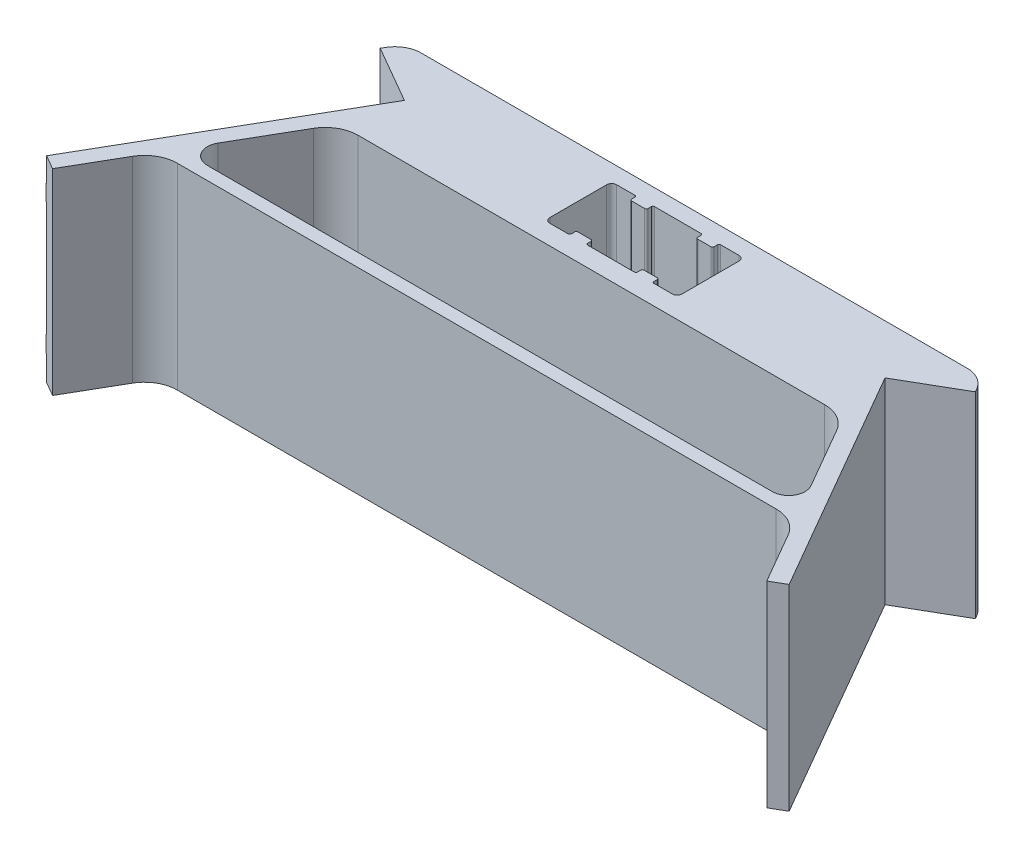
SolidWorks part; units mm, degrees
ref_plane "Front Plane" through (0, 0, 0) normal (0, 0, 1) x (1, 0, 0)
ref_plane "Top Plane" through (0, 0, 0) normal (0, 1, 0) x (1, 0, 0)
ref_plane "Right Plane" through (0, 0, 0) normal (1, 0, 0) x (0, 0, -1)
sketch "Sketch1" plane through (0, 0, 0) normal (0, 1, 0) x (1, 0, 0)
  line L0 (0, -61.4) -> (0, -111.1933) construction
  line L1 (0, 0) -> (-7.6, 0) construction
  line L2 (0, 0) -> (0, -20.4) construction
  line L3 (0, -20.4) -> (-7.1, -20.4) construction
  line L4 (-20.2, 0) -> (-20.2, -20.4) construction
  line L5 (0, 5) -> (-83.3812, 5)
  line L6 (-90.3094, 1) -> (-90.8868, 0)
  line L7 (-90.8868, 0) -> (-73.393, -10.1)
  line L8 (-73.393, -10.1) -> (-113.393, -79.382)
  line L9 (-113.393, -79.382) -> (-109.0629, -81.882)
  line L10 (-109.0629, -81.882) -> (-100.1244, -66.4)
  line L11 (-71.2568, -26.4) -> (0, -26.4)
  line L13 (0, -20.4) -> (-7.1, -20.4)
  line L14 (-20.2, -18.9) -> (-20.2, -1.5)
  line L15 (-18.7, 0) -> (-13.1, 0)
  line L16 (-86.2679, -57.4) -> (0, -57.4)
  line L18 (0, -61.4) -> (-91.4641, -61.4)
  line L19 (-90.5981, -49.9) -> (-79.9171, -31.4)
  line L20 (0, 0) -> (0, -20.4) construction
  line L21 (-7.6, -0.5) -> (-7.6, -1.5)
  line L22 (-20.2, -10.2) -> (0, -10.2) construction
  line L23 (-8.1, -2) -> (-12.1, -2)
  line L24 (-12.6, -0.5) -> (-12.6, -1.5)
  line L25 (-12.6, -19.9) -> (-12.6, -18.9)
  line L26 (-8.1, -18.4) -> (-12.1, -18.4)
  line L27 (-12.6, 0) -> (-20.2, 0) construction
  line L28 (-7.1, 0) -> (0, 0)
  line L29 (-7.6, -19.9) -> (-7.6, -18.9)
  line L30 (-13.1, -20.4) -> (-20.2, -20.4) construction
  line L31 (-13.1, -20.4) -> (-18.7, -20.4)
  line L32 (0, -26.4) -> (0, -57.4) construction
  arc A0 (-91.4641, -61.4) -> (-100.1244, -66.4) centre (-91.4641, -71.4) ccw
  arc A1 (-79.9171, -31.4) -> (-71.2568, -26.4) centre (-71.2568, -36.4) cw
  arc A2 (-86.2679, -57.4) -> (-90.5981, -49.9) centre (-86.2679, -52.4) cw
  arc A3 (-83.3812, 5) -> (-90.3094, 1) centre (-83.3812, -3) ccw
  arc A4 (-7.1, 0) -> (-7.6, -0.5) centre (-7.1, -0.5) ccw
  arc A5 (-12.6, -0.5) -> (-13.1, 0) centre (-13.1, -0.5) ccw
  arc A6 (-7.6, -1.5) -> (-8.1, -2) centre (-8.1, -1.5) cw
  arc A7 (-12.1, -2) -> (-12.6, -1.5) centre (-12.1, -1.5) cw
  arc A8 (-20.2, -1.5) -> (-18.7, 0) centre (-18.7, -1.5) cw
  arc A9 (-18.7, -20.4) -> (-20.2, -18.9) centre (-18.7, -18.9) cw
  arc A10 (-12.1, -18.4) -> (-12.6, -18.9) centre (-12.1, -18.9) ccw
  arc A11 (-7.6, -18.9) -> (-8.1, -18.4) centre (-8.1, -18.9) ccw
  arc A12 (-12.6, -19.9) -> (-13.1, -20.4) centre (-13.1, -19.9) cw
  arc A13 (-7.1, -20.4) -> (-7.6, -19.9) centre (-7.1, -19.9) cw
  point P24 (-94.9282, -57.4)
  point P27 (-88, 5)
  point P30 (-10.1, 0)
  point P63 (-10.1, -20.4)
  dimension "D13" = 10
  dimension "D14" = 5
  dimension "D15" = 8
  dimension "D17" = 0.5
  dimension "D18" = 1.5
  dimension "D1" = 20.2
  dimension "D2" = 20.4
  dimension "D3" = 5
  dimension "D4" = 88
  dimension "D5" = 120
  dimension "D6" = 5
  dimension "D7" = 20.2
  dimension "D8" = 80
  dimension "D9" = 5
  dimension "D10" = 6
  dimension "D11" = 4
  dimension "D12" = 37
  dimension "D16" = 5
sketch "Sketch5" plane through (0, 0, 0) normal (0, 1, 0) x (1, 0, 0)
  line L0 (0, -20.4) -> (-7.1, -20.4) construction
  line L1 (-7.6, -19.9) -> (-7.6, -18.9) construction
  line L2 (-8.1, -18.4) -> (-12.1, -18.4) construction
  line L3 (-12.6, -19.9) -> (-12.6, -18.9) construction
  line L4 (-13.1, -20.4) -> (-18.7, -20.4) construction
  line L5 (-20.2, -18.9) -> (-20.2, -1.5) construction
  line L6 (-18.7, 0) -> (-13.1, 0) construction
  line L7 (-12.6, -0.5) -> (-12.6, -1.5) construction
  line L8 (-8.1, -2) -> (-12.1, -2) construction
  line L9 (-7.6, -0.5) -> (-7.6, -1.5) construction
  line L10 (-7.1, 0) -> (0, 0) construction
  line L11 (-71.2568, -26.4) -> (0, -26.4) construction
  line L12 (-90.5981, -49.9) -> (-79.9171, -31.4) construction
  line L13 (-86.2679, -57.4) -> (0, -57.4) construction
  line L14 (0, 5) -> (-83.3812, 5) construction
  line L15 (-90.3094, 1) -> (-90.8868, 0) construction
  line L16 (-90.8868, 0) -> (-73.393, -10.1) construction
  line L17 (-73.393, -10.1) -> (-113.393, -79.382) construction
  line L18 (-113.393, -79.382) -> (-109.0629, -81.882) construction
  line L19 (-109.0629, -81.882) -> (-100.1244, -66.4) construction
  line L20 (0, -61.4) -> (-91.4641, -61.4) construction
  line L21 (7.1, -20.4) -> (-7.1, -20.4)
  line L22 (-7.6, -19.9) -> (-7.6, -18.9)
  line L23 (-8.1, -18.4) -> (-12.1, -18.4)
  line L24 (-12.6, -19.9) -> (-12.6, -18.9)
  line L25 (-13.1, -20.4) -> (-18.7, -20.4)
  line L26 (-20.2, -18.9) -> (-20.2, -1.5)
  line L27 (-18.7, 0) -> (-13.1, 0)
  line L28 (-12.6, -0.5) -> (-12.6, -1.5)
  line L29 (-8.1, -2) -> (-12.1, -2)
  line L30 (-7.6, -0.5) -> (-7.6, -1.5)
  line L31 (-7.1, 0) -> (7.1, 0)
  line L32 (-71.2568, -26.4) -> (71.2568, -26.4)
  line L33 (-90.5981, -49.9) -> (-79.9171, -31.4)
  line L34 (-86.2679, -57.4) -> (86.2679, -57.4)
  line L35 (83.3812, 5) -> (-83.3812, 5)
  line L36 (-90.3094, 1) -> (-90.8868, 0)
  line L37 (-90.8868, 0) -> (-73.393, -10.1)
  line L38 (-73.393, -10.1) -> (-113.393, -79.382)
  line L39 (-113.393, -79.382) -> (-109.0629, -81.882)
  line L40 (-109.0629, -81.882) -> (-100.1244, -66.4)
  line L41 (91.4641, -61.4) -> (-91.4641, -61.4)
  line L42 (0, 0) -> (0, -111.1933) construction
  line L43 (109.0629, -81.882) -> (100.1244, -66.4)
  line L44 (113.393, -79.382) -> (109.0629, -81.882)
  line L45 (73.393, -10.1) -> (113.393, -79.382)
  line L46 (90.8868, 0) -> (73.393, -10.1)
  line L47 (90.3094, 1) -> (90.8868, 0)
  line L48 (90.5981, -49.9) -> (79.9171, -31.4)
  line L49 (7.6, -0.5) -> (7.6, -1.5)
  line L50 (8.1, -2) -> (12.1, -2)
  line L51 (12.6, -0.5) -> (12.6, -1.5)
  line L52 (18.7, 0) -> (13.1, 0)
  line L53 (20.2, -18.9) -> (20.2, -1.5)
  line L54 (13.1, -20.4) -> (18.7, -20.4)
  line L55 (12.6, -19.9) -> (12.6, -18.9)
  line L56 (8.1, -18.4) -> (12.1, -18.4)
  line L57 (7.6, -19.9) -> (7.6, -18.9)
  arc A0 (-7.6, -19.9) -> (-7.1, -20.4) centre (-7.1, -19.9) ccw construction
  arc A1 (-7.6, -18.9) -> (-8.1, -18.4) centre (-8.1, -18.9) ccw construction
  arc A2 (-12.1, -18.4) -> (-12.6, -18.9) centre (-12.1, -18.9) ccw construction
  arc A3 (-13.1, -20.4) -> (-12.6, -19.9) centre (-13.1, -19.9) ccw construction
  arc A4 (-20.2, -18.9) -> (-18.7, -20.4) centre (-18.7, -18.9) ccw construction
  arc A5 (-18.7, 0) -> (-20.2, -1.5) centre (-18.7, -1.5) ccw construction
  arc A6 (-12.6, -0.5) -> (-13.1, 0) centre (-13.1, -0.5) ccw construction
  arc A7 (-12.6, -1.5) -> (-12.1, -2) centre (-12.1, -1.5) ccw construction
  arc A8 (-8.1, -2) -> (-7.6, -1.5) centre (-8.1, -1.5) ccw construction
  arc A9 (-7.1, 0) -> (-7.6, -0.5) centre (-7.1, -0.5) ccw construction
  arc A10 (-71.2568, -26.4) -> (-79.9171, -31.4) centre (-71.2568, -36.4) ccw construction
  arc A11 (-90.5981, -49.9) -> (-86.2679, -57.4) centre (-86.2679, -52.4) ccw construction
  arc A12 (-83.3812, 5) -> (-90.3094, 1) centre (-83.3812, -3) ccw construction
  arc A13 (-91.4641, -61.4) -> (-100.1244, -66.4) centre (-91.4641, -71.4) ccw construction
  arc A14 (-7.6, -19.9) -> (-7.1, -20.4) centre (-7.1, -19.9) ccw
  arc A15 (-7.6, -18.9) -> (-8.1, -18.4) centre (-8.1, -18.9) ccw
  arc A16 (-12.1, -18.4) -> (-12.6, -18.9) centre (-12.1, -18.9) ccw
  arc A17 (-13.1, -20.4) -> (-12.6, -19.9) centre (-13.1, -19.9) ccw
  arc A18 (-20.2, -18.9) -> (-18.7, -20.4) centre (-18.7, -18.9) ccw
  arc A19 (-18.7, 0) -> (-20.2, -1.5) centre (-18.7, -1.5) ccw
  arc A20 (-12.6, -0.5) -> (-13.1, 0) centre (-13.1, -0.5) ccw
  arc A21 (-12.6, -1.5) -> (-12.1, -2) centre (-12.1, -1.5) ccw
  arc A22 (-8.1, -2) -> (-7.6, -1.5) centre (-8.1, -1.5) ccw
  arc A23 (-7.1, 0) -> (-7.6, -0.5) centre (-7.1, -0.5) ccw
  arc A24 (-71.2568, -26.4) -> (-79.9171, -31.4) centre (-71.2568, -36.4) ccw
  arc A25 (-90.5981, -49.9) -> (-86.2679, -57.4) centre (-86.2679, -52.4) ccw
  arc A26 (-83.3812, 5) -> (-90.3094, 1) centre (-83.3812, -3) ccw
  arc A27 (-91.4641, -61.4) -> (-100.1244, -66.4) centre (-91.4641, -71.4) ccw
  arc A28 (91.4641, -61.4) -> (100.1244, -66.4) centre (91.4641, -71.4) cw
  arc A29 (83.3812, 5) -> (90.3094, 1) centre (83.3812, -3) cw
  arc A30 (90.5981, -49.9) -> (86.2679, -57.4) centre (86.2679, -52.4) cw
  arc A31 (71.2568, -26.4) -> (79.9171, -31.4) centre (71.2568, -36.4) cw
  arc A32 (7.1, 0) -> (7.6, -0.5) centre (7.1, -0.5) cw
  arc A33 (8.1, -2) -> (7.6, -1.5) centre (8.1, -1.5) cw
  arc A34 (12.6, -1.5) -> (12.1, -2) centre (12.1, -1.5) cw
  arc A35 (12.6, -0.5) -> (13.1, 0) centre (13.1, -0.5) cw
  arc A36 (18.7, 0) -> (20.2, -1.5) centre (18.7, -1.5) cw
  arc A37 (20.2, -18.9) -> (18.7, -20.4) centre (18.7, -18.9) cw
  arc A38 (13.1, -20.4) -> (12.6, -19.9) centre (13.1, -19.9) cw
  arc A39 (12.1, -18.4) -> (12.6, -18.9) centre (12.1, -18.9) cw
  arc A40 (7.6, -18.9) -> (8.1, -18.4) centre (8.1, -18.9) cw
  arc A41 (7.6, -19.9) -> (7.1, -20.4) centre (7.1, -19.9) cw
extrude "Boss-Extrude3" add sketch "Sketch5" along normal blind 60
sketch "Sketch6" plane through (-50.6714, 0, -29.2551) normal (-0.866, 0, -0.5) x (-0.5, 0, 0.866)
  line L0 (45.4434, 60) -> (45.4434, 0) construction
  line L1 (45.4434, 52.5) -> (125.4434, 52.5)
  line L2 (45.4434, 52.5) -> (45.4434, 47.5)
  line L3 (45.4434, 47.5) -> (125.4434, 47.5)
  line L4 (125.4434, 52.5) -> (125.4434, 47.5)
  line L5 (125.4434, 60) -> (125.4434, 0) construction
  line L6 (45.4434, 60) -> (125.4434, 60) construction
  line L7 (45.4434, 30) -> (125.4434, 30) construction
  line L8 (125.4434, 7.5) -> (125.4434, 12.5)
  line L9 (45.4434, 12.5) -> (125.4434, 12.5)
  line L10 (45.4434, 7.5) -> (45.4434, 12.5)
  line L11 (45.4434, 7.5) -> (125.4434, 7.5)
  dimension "D1" = 5
  dimension "D2" = 7.5
extrude "Boss-Extrude4" add sketch "Sketch6" along normal blind 0.5
